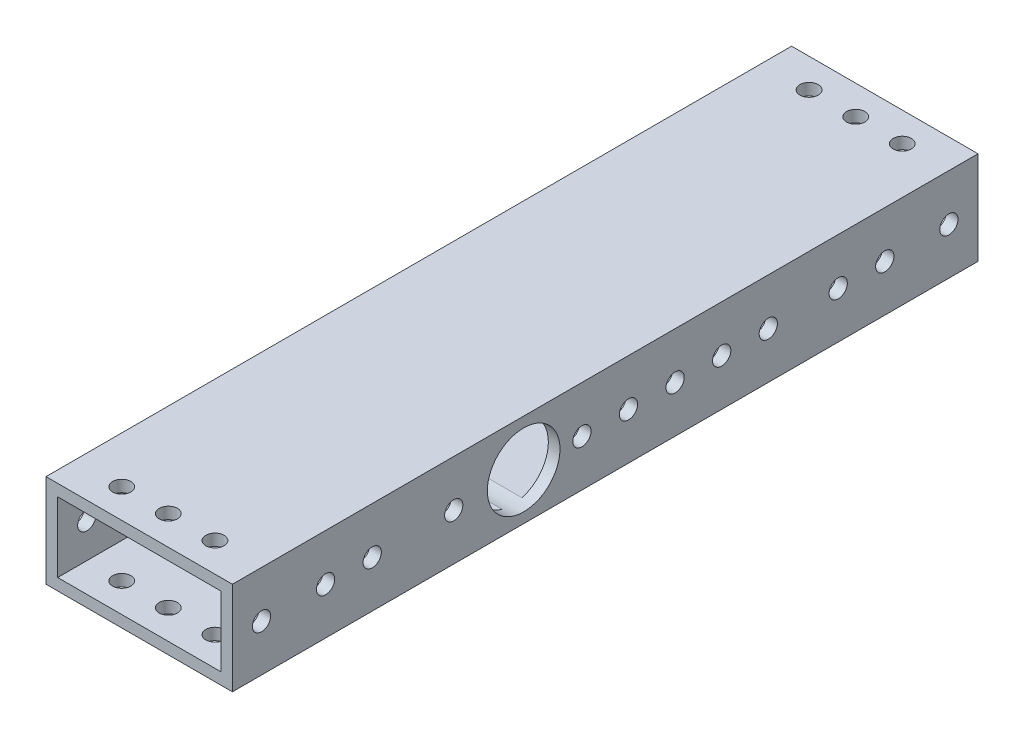
SolidWorks part; units mm, degrees
material "6061-T6 (SS)"
ref_plane "Front Plane" through (0, 0, 0) normal (0, 0, 1) x (1, 0, 0)
ref_plane "Top Plane" through (0, 0, 0) normal (0, 1, 0) x (1, 0, 0)
ref_plane "Right Plane" through (0, 0, 0) normal (1, 0, 0) x (0, 0, -1)
sketch "Sketch1" plane through (0, 0, 0) normal (0, 0, 1) x (1, 0, 0)
  line L0 (-22.225, 9.525) -> (22.225, 9.525)
  line L1 (-25.4, -12.7) -> (25.4, -12.7)
  line L2 (-25.4, -12.7) -> (-25.4, 12.7)
  line L3 (-25.4, 12.7) -> (25.4, 12.7)
  line L4 (25.4, -12.7) -> (25.4, 12.7)
  line L5 (-25.4, -12.7) -> (25.4, 12.7) construction
  line L6 (-25.4, 12.7) -> (25.4, -12.7) construction
  line L7 (22.225, -9.525) -> (22.225, 9.525)
  line L8 (-22.225, -9.525) -> (22.225, -9.525)
  line L9 (-22.225, -9.525) -> (-22.225, 9.525)
  point P0 (0, 0)
  dimension "D1" = 50.8
  dimension "D2" = 25.4
  dimension "D3" = 3.175
extrude "Boss-Extrude1" add sketch "Sketch1" along normal mid plane 203.2
sketch "Sketch3" plane through (0, 12.7, 0) normal (0, 1, 0) x (1, 0, 0)
  line L0 (-25.4, 0) -> (25.4, 0) construction
  line L1 (-25.4, -101.6) -> (-25.4, 101.6) construction
  line L2 (25.4, -101.6) -> (25.4, 101.6) construction
  line L3 (25.4, -101.6) -> (-25.4, -101.6) construction
  circle A0 centre (-12.7, -93.6625) radius 2.4892
  circle A1 centre (0, -93.6625) radius 2.4892
  circle A2 centre (12.7, -93.6625) radius 2.4892
  circle A3 centre (12.7, 93.6625) radius 2.4892
  circle A4 centre (0, 93.6625) radius 2.4892
  circle A5 centre (-12.7, 93.6625) radius 2.4892
  dimension "D1" = 4.9784
  dimension "D2" = 12.7
  dimension "D3" = 12.7
  dimension "D4" = 7.9375
extrude "Cut-Extrude2" cut sketch "Sketch3" against normal through all
sketch "Sketch4" plane through (25.4, 0, 0) normal (1, 0, 0) x (0, 0, -1)
  line L0 (-22.225, 0) -> (-45.1908, 0) construction
  line L1 (-12.319, 0) -> (-32.131, 0) construction
  line L8 (-22.225, 0) -> (31.75, 0) construction
  line L9 (0, 12.7) -> (0, -12.7) construction
  line L10 (-101.6, 12.7) -> (101.6, 12.7) construction
  line L11 (-101.6, -12.7) -> (101.6, -12.7) construction
  circle A0 centre (-22.225, 0) radius 9.906
  circle A9 centre (31.75, 0) radius 2.4892
  circle A10 centre (19.05, 0) radius 2.4892
  dimension "D2" = 19.812
  dimension "D3" = 22.225
  dimension "D1" = 53.975
  dimension "D4" = 4.9784
  dimension "D6" = 41.275
extrude "Cut-Extrude3" cut sketch "Sketch4" against normal through all
sketch "Sketch2" plane through (25.4, 0, 0) normal (1, 0, 0) x (0, 0, -1)
  line L0 (-101.6, -12.7) -> (-101.6, 12.7) construction
  line L1 (0, 12.7) -> (0, -12.7) construction
  line L2 (-101.6, 12.7) -> (101.6, 12.7) construction
  line L3 (-101.6, -12.7) -> (101.6, -12.7) construction
  circle A0 centre (-93.6625, 0) radius 2.4892
  circle A1 centre (93.6625, 0) radius 2.4892
  circle A2 centre (-76.2, 0) radius 2.4892
  circle A3 centre (-63.5, 0) radius 2.4892
  circle A4 centre (63.5, 0) radius 2.4892
  circle A5 centre (76.2, 0) radius 2.4892
  dimension "D2" = 4.9784
  dimension "D5" = 4.9784
  dimension "D4" = 25.4
  dimension "D1" = 7.9375
  dimension "D3" = 12.7
extrude "Cut-Extrude1" cut sketch "Sketch2" against normal through all
sketch "Sketch5" plane through (0, -12.7, 0) normal (0, -1, 0) x (1, 0, 0)
  line L0 (-25.4, 101.6) -> (-25.4, -101.6) construction
  line L1 (-25.4, 101.6) -> (25.4, 101.6) construction
  line L4 (25.4, 22.225) -> (-25.4, 22.225) construction
  line L5 (25.4, 101.6) -> (25.4, -101.6) construction
  circle A0 centre (-3.175, 66.675) radius 2.4892
  circle A1 centre (-15.875, 66.675) radius 2.4892
  circle A2 centre (-15.875, 53.975) radius 2.4892
  circle A3 centre (-3.175, 53.975) radius 2.4892
  circle A8 centre (-3.175, -9.525) radius 2.4892
  circle A9 centre (-15.875, -9.525) radius 2.4892
  circle A10 centre (-15.875, -22.225) radius 2.4892
  circle A11 centre (-3.175, -22.225) radius 2.4892
  dimension "D3" = 4.9784
  dimension "D4" = 9.525
  dimension "D7" = 12.7
  dimension "D12" = 79.375
  dimension "D5" = 31.75
  dimension "D6" = 12.7
  dimension "D1" = 2
  dimension "D2" = 2
extrude "Cut-Extrude4" cut sketch "Sketch5" against normal up to next
sketch "Sketch7" plane through (25.4, 0, 0) normal (1, 0, 0) x (0, 0, -1)
  circle A0 centre (44.45, 0) radius 2.4892
  circle A1 centre (31.75, 0) radius 2.4892 construction
  circle A5 centre (6.35, 0) radius 2.4892
  circle A6 centre (-6.35, 0) radius 2.4892
  circle A7 centre (-41.275, 0) radius 2.4892
  circle A8 centre (-22.225, 0) radius 9.906 construction
  dimension "D1" = 12.7
  dimension "D2" = 19.05
  dimension "D3" = 15.875
  dimension "D4" = 12.7
  dimension "D5" = 4.9784
extrude "Cut-Extrude5" cut sketch "Sketch7" against normal up to next contours A0 | A7 | A6 | A5
